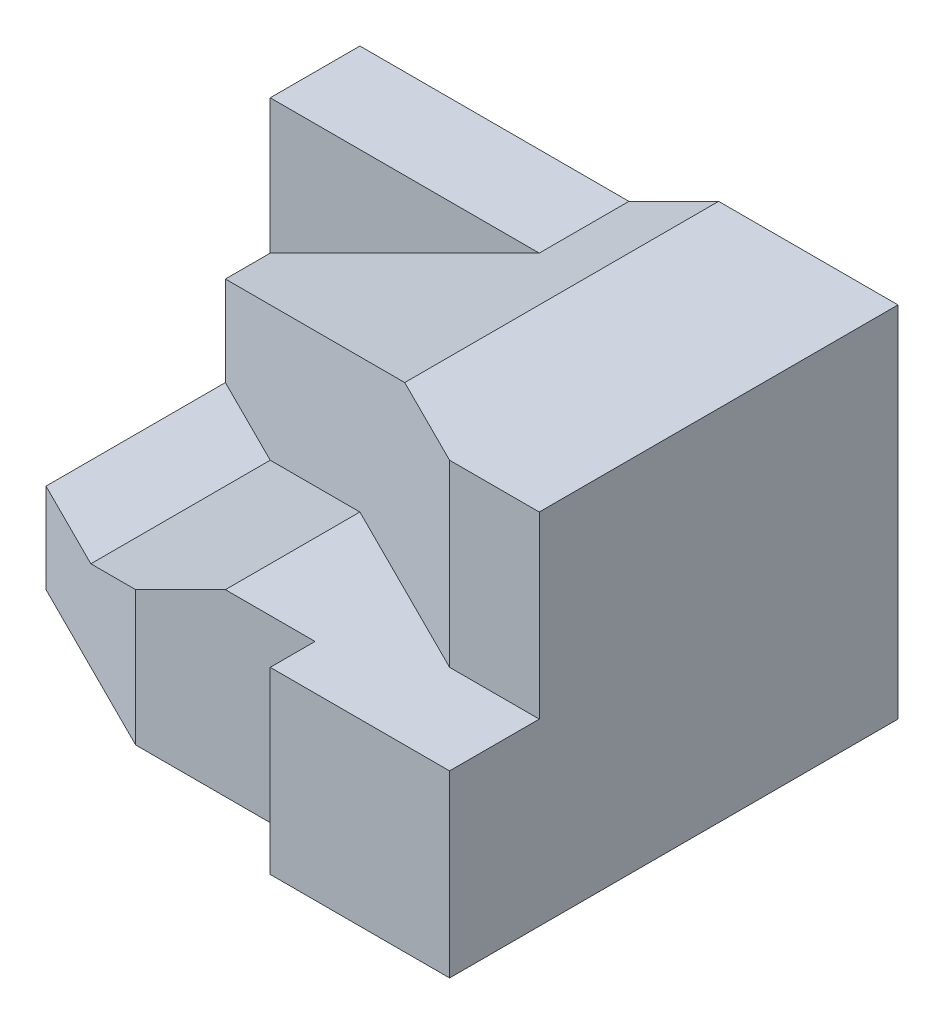
SolidWorks part; units mm, degrees
ref_plane "Front Plane" through (0, 0, 0) normal (0, 0, 1) x (1, 0, 0)
ref_plane "Top Plane" through (0, 0, 0) normal (0, 1, 0) x (1, 0, 0)
ref_plane "Right Plane" through (0, 0, 0) normal (1, 0, 0) x (0, 0, -1)
sketch "Sketch1" plane through (0, 0, 0) normal (0, 1, 0) x (1, 0, 0)
  line L1 (0, 0) -> (120, 0)
  line L2 (0, 0) -> (0, 100)
  line L3 (0, 100) -> (120, 100)
  line L4 (120, 0) -> (120, 100)
  dimension "D1" = 120
  dimension "D2" = 100
extrude "Boss-Extrude1" add sketch "Sketch1" along normal blind 20
sketch "Sketch2" plane through (0, 20, 0) normal (0, 1, 0) x (1, 0, 0)
  line L0 (0, 30) -> (40, 10)
  line L1 (0, 100) -> (0, 0) construction
  line L2 (40, 10) -> (80, 10)
  line L3 (80, 10) -> (80, 0)
  line L4 (0, 0) -> (120, 0) construction
  line L5 (80, 0) -> (0, 0)
  line L6 (0, 0) -> (0, 30)
  dimension "D1" = 30
  dimension "D2" = 10
  dimension "D3" = 40
  dimension "D4" = 20
  dimension "D5" = 40
extrude "Cut-Extrude1" cut sketch "Sketch2" against normal blind 20
sketch "Sketch3" plane through (0, 0, 0) normal (0, 0, 1) x (1, 0, 0)
  line L1 (120, 0) -> (80, 0)
  line L2 (120, 0) -> (120, 40)
  line L3 (120, 40) -> (80, 40)
  line L4 (80, 0) -> (80, 40)
  dimension "D1" = 40
  dimension "D2" = 40
extrude "Boss-Extrude3" add sketch "Sketch3" against normal blind 100
sketch "Sketch4" plane through (0, 0, -10) normal (0, 0, 1) x (1, 0, 0)
  line L0 (80, 20) -> (80, 40)
  line L1 (80, 40) -> (60, 40)
  line L2 (60, 40) -> (40, 30)
  line L3 (40, 30) -> (40, 20)
  line L4 (40, 20) -> (80, 20)
  dimension "D1" = 20
  dimension "D2" = 20
  dimension "D3" = 10
extrude "Boss-Extrude4" add sketch "Sketch4" against normal blind 90
ref_plane "Plane1" through (0, 0, -20) normal (0, 0, 1) x (1, 0, 0)
sketch "Sketch5" plane through (0, 0, -20) normal (0, 0, 1) x (1, 0, 0)
  line L1 (120, 40) -> (100, 40)
  line L2 (120, 40) -> (120, 80)
  line L3 (120, 80) -> (100, 80)
  line L4 (100, 40) -> (100, 80)
  dimension "D1" = 20
  dimension "D2" = 40
extrude "Boss-Extrude6" add sketch "Sketch5" against normal blind 80
sketch "Sketch6" plane through (0, 80, 0) normal (0, 1, 0) x (1, 0, 0)
  line L0 (100, 100) -> (80, 100)
  line L1 (80, 100) -> (80, 30)
  line L2 (80, 30) -> (100, 20)
  line L3 (100, 20) -> (100, 100)
  dimension "D1" = 20
  dimension "D2" = 10
extrude "Boss-Extrude7" add sketch "Sketch6" against normal blind 80
sketch "Sketch7" plane through (0, 0, -100) normal (0, 0, -1) x (-1, 0, 0)
  line L1 (0, 20) -> (-60, 20)
  line L2 (0, 20) -> (0, 70)
  line L3 (0, 70) -> (-60, 70)
  line L4 (-60, 20) -> (-60, 70)
  dimension "D1" = 60
  dimension "D2" = 50
extrude "Boss-Extrude8" add sketch "Sketch7" against normal blind 20
sketch "Sketch8" plane through (0, 0, -80) normal (0, 0, 1) x (1, 0, 0)
  line L1 (0, 20) -> (10, 20)
  line L2 (0, 20) -> (0, 40)
  line L3 (0, 40) -> (10, 40)
  line L4 (10, 20) -> (10, 40)
  dimension "D1" = 10
  dimension "D2" = 20
extrude "Boss-Extrude9" add sketch "Sketch8" along normal blind 10
ref_plane "Plane2" through (-16, 32, 0) normal (0.4472, -0.8944, 0) x (-0.8944, -0.4472, 0)
sketch "Sketch9" plane through (-16, 32, 0) normal (0.4472, -0.8944, 0) x (-0.8944, -0.4472, 0)
  line L0 (-107.3313, 100) -> (-107.3313, 30)
  line L1 (-107.3313, 30) -> (-17.8885, 70)
  line L2 (-17.8885, 70) -> (-17.8885, 80)
  line L3 (-17.8885, 80) -> (-107.3313, 100)
extrude "Boss-Extrude10" add sketch "Sketch9" along normal blind 42
sketch "Sketch11" plane through (0, 0, -100) normal (0, 0, -1) x (-1, 0, 0)
  line L0 (-80, 40) -> (-60, 40)
  line L1 (-60, 40) -> (-60, 70)
  line L2 (-60, 70) -> (-80, 80)
  line L3 (-80, 80) -> (-80, 40)
extrude "Boss-Extrude18" add sketch "Sketch11" against normal blind 42
ref_plane "Plane3" through (28, 0, -56) normal (-0.4472, 0, 0.8944) x (0.8944, 0, 0.4472)
sketch "Sketch12" plane through (28, 0, -56) normal (-0.4472, 0, 0.8944) x (0.8944, 0, 0.4472)
  line L0 (58.1378, 80) -> (58.1378, 40)
  line L1 (58.1378, 40) -> (-31.305, 20)
  line L2 (-31.305, 20) -> (-31.305, 40)
  line L3 (-31.305, 40) -> (58.1378, 80)
extrude "Boss-Extrude19" add sketch "Sketch12" against normal blind 30
ref_plane "Plane4" through (-4.4645, 9.1826, -0.5073) normal (0.4367, -0.8982, 0.0496) x (-0.8996, -0.436, 0.0241)
sketch "Sketch17" plane through (28, 0, -56) normal (-0.4472, 0, 0.8944) x (0.8944, 0, 0.4472)
  line L0 (13.4164, 30) -> (-31.305, 20)
  line L1 (-31.305, 20) -> (13.4164, 20)
  line L2 (13.4164, 20) -> (13.4164, 30)
extrude "Boss-Extrude21" add sketch "Sketch17" against normal blind 30
sketch "Sketch18" plane through (0, 20, 0) normal (0, 1, 0) x (1, 0, 0)
  line L0 (20, 60) -> (20, 20)
  line L1 (0, 70) -> (40, 50) construction
  line L2 (40, 10) -> (0, 30) construction
ref_plane "Plane5" through (-4, 8, 0) normal (-0.4472, 0.8944, 0) x (0.8944, 0.4472, 0)
sketch "Sketch19" plane through (-4, 8, 0) normal (-0.4472, 0.8944, 0) x (0.8944, 0.4472, 0)
  line L0 (26.8328, 20) -> (71.5542, 10)
  line L1 (71.5542, 10) -> (71.5542, 40)
  line L2 (71.5542, 40) -> (26.8328, 60)
  line L3 (26.8328, 60) -> (26.8328, 20)
extrude "Boss-Extrude22" add sketch "Sketch19" against normal blind 30
sketch "Sketch20" plane through (-4, 8, 0) normal (-0.4472, 0.8944, 0) x (0.8944, 0.4472, 0)
  line L0 (49.1935, 10) -> (26.8328, 20)
  line L1 (26.8328, 20) -> (49.1935, 15)
  line L2 (49.1935, 15) -> (49.1935, 10)
extrude "Boss-Extrude23" add sketch "Sketch20" against normal blind 30
sketch "Sketch21" plane through (12, 0, -24) normal (-0.4472, 0, 0.8944) x (0.8944, 0, 0.4472)
  line L0 (8.9443, 20) -> (31.305, 30)
  line L1 (31.305, 30) -> (31.305, 20)
  line L2 (31.305, 20) -> (8.9443, 20)
extrude "Boss-Extrude24" add sketch "Sketch21" against normal blind 30
sketch "Sketch22" plane through (0, 0, 0) normal (0, -1, 0) x (1, 0, 0)
  line L1 (0, -100) -> (120, -100)
  line L2 (0, -100) -> (0, 0)
  line L3 (0, 0) -> (120, 0)
  line L4 (120, -100) -> (120, 0)
extrude "Cut-Extrude3" cut sketch "Sketch22" along normal blind 30
equation "\"ft\"=90"
